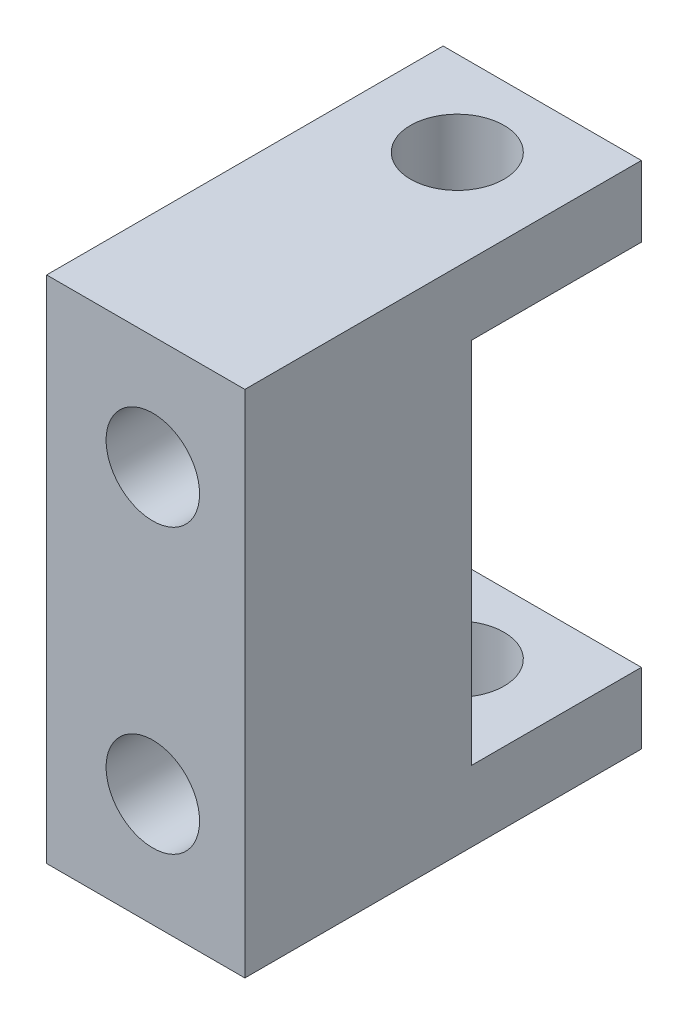
SolidWorks part; units mm, degrees
material "1060 Alloy"
ref_plane "Front Plane" through (0, 0, 0) normal (0, 0, 1) x (1, 0, 0)
ref_plane "Top Plane" through (0, 0, 0) normal (0, 1, 0) x (1, 0, 0)
ref_plane "Right Plane" through (0, 0, 0) normal (1, 0, 0) x (0, 0, -1)
sketch "Sketch1" plane through (0, 0, 0) normal (0, 0, 1) x (1, 0, 0)
  line L0 (-7, 0) -> (0, 0)
  line L1 (0, 0) -> (0, 18)
  line L3 (-7, 18) -> (-7, 0)
  line L6 (-7, 18) -> (0, 18)
  dimension "D2" = 7
  dimension "D4" = 18
extrude "Extrude1" add sketch "Sketch1" along normal blind 8
ref_plane "Plane1" through (0, 0, -19) normal (0, 0, 1) x (1, 0, 0)
hole_wizard "M4x0.7 Tapped Hole1" positions "3DSketch1" profile "Sketch6" tap size "M4x0.7" standard "Ansi Metric" end condition through all
sketch3d "3DSketch1"
  line L9 (-7, 18, 8) -> (-7, 0, 8) construction
  line L10 (-7, 0, 8) -> (0, 0, 8) construction
  line L11 (0, 18, 8) -> (-7, 18, 8) construction
  point P4 (-3.25, 4, 8)
  point P6 (-3.25, 14, 8)
  dimension "D1" = 3.75
  dimension "D2" = 4
  dimension "D3" = 4
  dimension "D7" = 10
sketch "Sketch6" plane through (-3.25, 4, 8) normal (1, 0, 0) x (0, -1, 0)
  line L0 (0, 0) -> (0, 8)
  line L1 (0, 8) -> (1.65, 8)
  line L2 (1.65, 8) -> (1.65, 0)
  line L5 (1.65, 0) -> (0, 0)
  line L11 (0, -6.35) -> (0, 107.95) construction
  dimension "Thru Tap Drill Dia." = 3.3
  dimension "Thru Tap Drill Depth" = 8
cosmetic thread "Hole Thread1" parameters "D2"=13.3
cosmetic thread "Hole Thread2" parameters "D2"=13.3
sketch "Sketch7" plane through (0, 0, 0) normal (0, 0, -1) x (-1, 0, 0)
  line L0 (7, 0) -> (7, 18) construction
  line L1 (0, 18) -> (7, 18)
  line L2 (0, 18) -> (0, 15.5)
  line L3 (0, 15.5) -> (7, 15.5)
  line L4 (7, 18) -> (7, 15.5)
  line L6 (0, 0) -> (7, 0)
  line L7 (0, 0) -> (0, 2.5)
  line L8 (0, 2.5) -> (7, 2.5)
  line L9 (7, 0) -> (7, 2.5)
  dimension "D3" = 2.5
  dimension "D4" = 2.5
extrude "Extrude5" add sketch "Sketch7" along normal blind 6
hole_wizard "M4x0.7 Tapped Hole2" positions "3DSketch2" profile "Sketch8" tap size "M4x0.7" standard "Ansi Metric"
sketch3d "3DSketch2"
  line L2 (-7, 18, -6) -> (0, 18, -6) construction
  line L3 (0, 18, 8) -> (0, 18, -6) construction
  point P0 (-3.5, 18, -3)
  point P6 (-3.5, 0, -3)
  dimension "D3" = 3
  dimension "D4" = 3.5
sketch "Sketch8" plane through (-3.5, 18, -3) normal (1, 0, 0) x (0, 0, 1)
  line L0 (0, 0) -> (0, 11.2914)
  line L1 (0, 11.2914) -> (1.65, 10.3)
  line L2 (1.65, 10.3) -> (1.65, 0)
  line L5 (1.65, 0) -> (0, 0)
  line L10 (0, 11.2914) -> (-1.65, 10.3) construction
  line L11 (0, -6.35) -> (0, 107.95) construction
  dimension "Tap Drill Dia." = 3.3
  dimension "Tap Drill Depth" = 10.3
  dimension "Drill Angle" = 118
cosmetic thread "Hole Thread3" parameters "D2"=13.3
cosmetic thread "Hole Thread4" parameters "D2"=13.3
